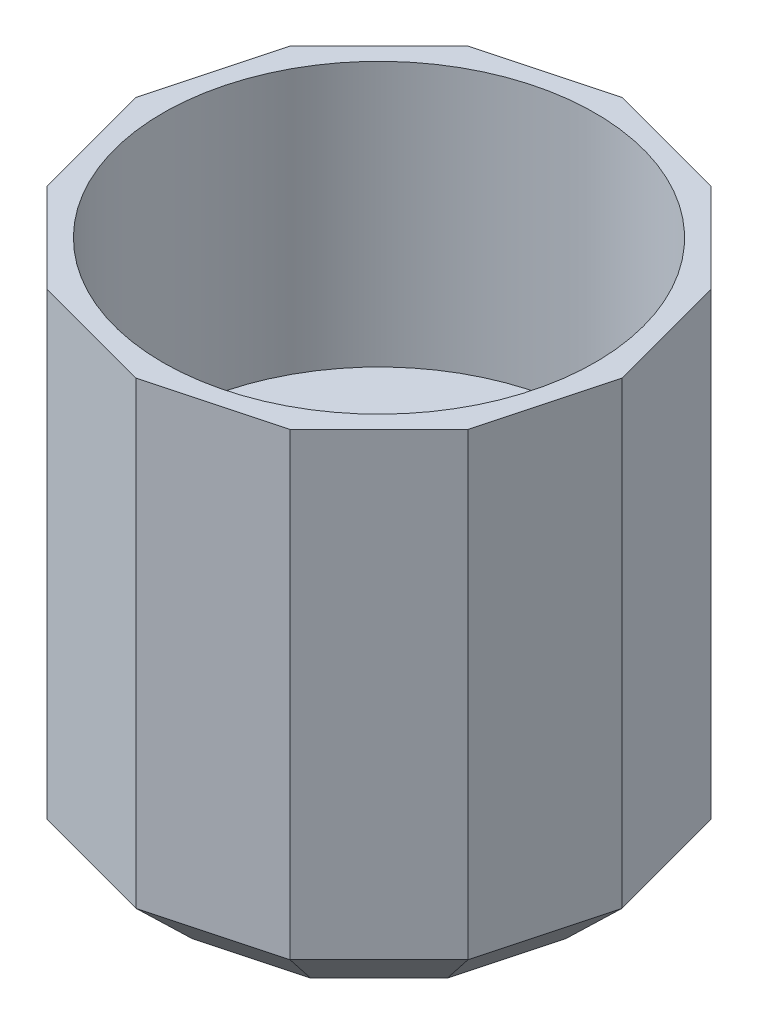
SolidWorks part; units mm, degrees
ref_plane "Front Plane" through (0, 0, 0) normal (0, 0, 1) x (1, 0, 0)
ref_plane "Top Plane" through (0, 0, 0) normal (0, 1, 0) x (1, 0, 0)
ref_plane "Right Plane" through (0, 0, 0) normal (1, 0, 0) x (0, 0, -1)
sketch "Sketch1" plane through (0, 0, 0) normal (0, 1, 0) x (1, 0, 0)
  line L1 (0, 9) -> (-4.5, 7.7942)
  line L2 (-4.5, 7.7942) -> (-7.7942, 4.5)
  line L3 (-7.7942, 4.5) -> (-9, 0)
  line L4 (-9, 0) -> (-7.7942, -4.5)
  line L5 (-7.7942, -4.5) -> (-4.5, -7.7942)
  line L6 (-4.5, -7.7942) -> (0, -9)
  line L7 (0, -9) -> (4.5, -7.7942)
  line L8 (4.5, -7.7942) -> (7.7942, -4.5)
  line L9 (7.7942, -4.5) -> (9, 0)
  line L10 (9, 0) -> (7.7942, 4.5)
  line L11 (7.7942, 4.5) -> (4.5, 7.7942)
  line L12 (4.5, 7.7942) -> (0, 9)
  circle A1 centre (0, 0) radius 8.6933 construction
extrude "Boss-Extrude1" add sketch "Sketch1" along normal blind 19
sketch "Sketch2" plane through (0, 19, 0) normal (0, 1, 0) x (1, 0, 0)
  circle A0 centre (0, 0) radius 8
extrude "Cut-Extrude1" cut sketch "Sketch2" against normal blind 9.8
sketch "Sketch3" plane through (0, 9.2, 0) normal (0, 1, 0) x (1, 0, 0)
  circle A0 centre (0, 0) radius 3.05
extrude "Cut-Extrude2" cut sketch "Sketch3" against normal blind 14
chamfer "Chamfer1" distance 2 angle 45 12 edges at (-6.1471, 0, 6.1471) (-2.25, 0, 8.3971) (2.25, 0, 8.3971) (6.1471, 0, 6.1471) (8.3971, 0, 2.25) (8.3971, 0, -2.25) (6.1471, 0, -6.1471) (2.25, 0, -8.3971) (-2.25, 0, -8.3971) (-6.1471, 0, -6.1471) (-8.3971, 0, -2.25) (-8.3971, 0, 2.25)
sketch "Sketch4" plane through (0, 1, 0) normal (0, 1, 0) x (1, 0, 0)
  circle A0 centre (0, 0) radius 3.3
extrude "Boss-Extrude2" add sketch "Sketch4" along normal blind 3.2
sketch "Sketch6" plane through (0, 4.2, 0) normal (0, 1, 0) x (1, 0, 0)
  line L2 (-0.4, 0) -> (-0.4, 3.8385)
  line L3 (-0.4, 3.8385) -> (0.4, 3.8385)
  line L4 (0.4, 3.8385) -> (0.4, -4.3536)
  line L5 (0.4, -4.3536) -> (-0.4, -4.3536)
  line L6 (-0.4, -4.3536) -> (-0.4, 0)
extrude "Boss-Extrude3" add sketch "Sketch6" along normal blind 4
sketch "Sketch7" plane through (0, 1, 0) normal (0, -1, 0) x (-1, 0, 0)
  circle A0 centre (0, 0) radius 3.05
extrude "Boss-Extrude4" add sketch "Sketch7" along normal up to surface (1 mm away) up to face at (0, 0, 0)
sketch "Sketch8" plane through (0, 4.2, 0) normal (0, 1, 0) x (1, 0, 0)
  circle A0 centre (0, 0) radius 3.05
extrude "Boss-Extrude5" add sketch "Sketch8" along normal blind 2
